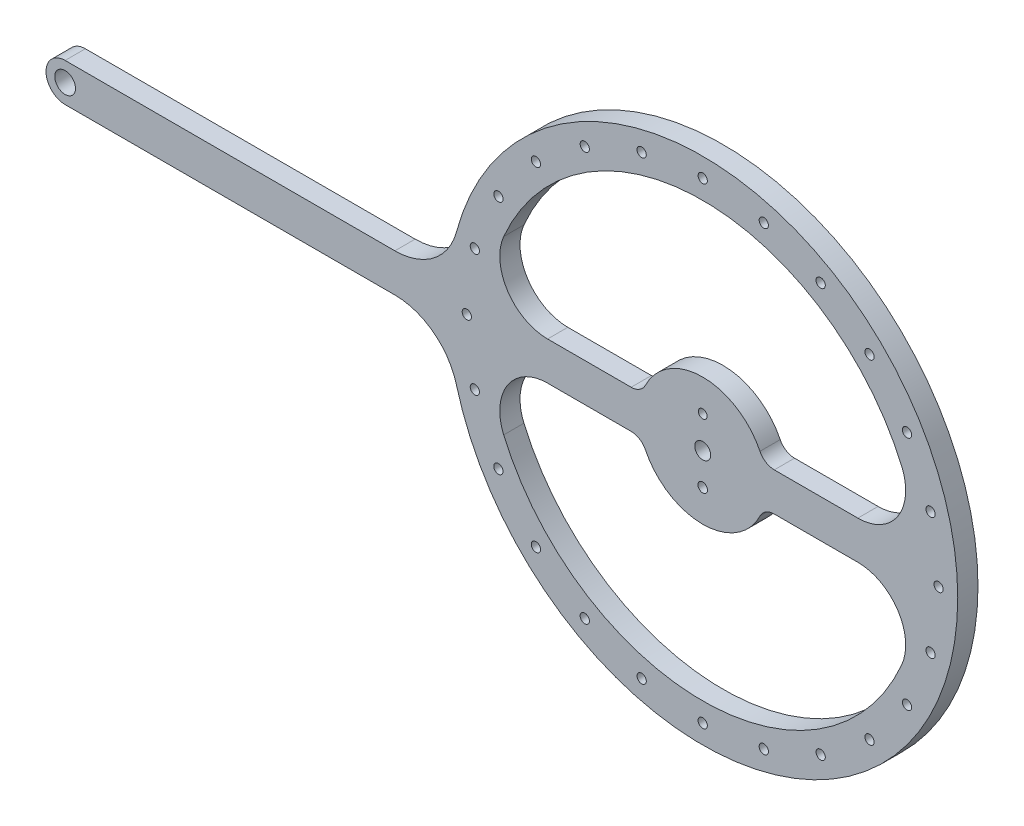
SolidWorks part; units mm, degrees
ref_plane "Front Plane" through (0, 0, 0) normal (0, 0, 1) x (1, 0, 0)
ref_plane "Top Plane" through (0, 0, 0) normal (0, 1, 0) x (1, 0, 0)
ref_plane "Right Plane" through (0, 0, 0) normal (1, 0, 0) x (0, 0, -1)
sketch "Sketch1" plane through (0, 0, 0) normal (0, 0, 1) x (1, 0, 0)
  line L0 (-155.3529, 10.2117) -> (-51.9137, 10.2117)
  line L1 (-4.015, 10.2117) -> (22.1972, 10.2117)
  line L2 (67.0971, 10.2117) -> (93.3092, 10.2117)
  line L3 (93.3092, 22.2117) -> (67.0971, 22.2117)
  line L4 (22.1972, 22.2117) -> (-4.015, 22.2117)
  line L5 (-51.9137, 22.2117) -> (-155.3529, 22.2117)
  arc A0 (-32.6016, -4.5883) -> (-51.9137, 10.2117) centre (-51.9137, -9.7883) ccw
  circle A1 centre (-19.4388, -20.7883) radius 1.45
  circle A2 centre (-26.8314, -2.9409) radius 1.45
  arc A3 (-51.9137, 22.2117) -> (-32.6016, 37.0117) centre (-51.9137, 42.2117) ccw
  arc A4 (-155.3529, 22.2117) -> (-155.3529, 10.2117) centre (-155.3529, 16.2117) ccw
  circle A5 centre (-155.3529, 16.2117) radius 3.25
  circle A6 centre (-26.8314, 35.3643) radius 1.45
  circle A7 centre (-19.4388, 53.2117) radius 1.45
  circle A8 centre (-29.3529, 16.2117) radius 1.45
  arc A9 (107.0815, -10.7317) -> (93.3092, 10.2117) centre (93.3092, -4.7883) ccw
  arc A10 (-4.015, 10.2117) -> (-17.7873, -10.7317) centre (-4.015, -4.7883) ccw
  arc A11 (67.0971, 10.2117) -> (62.6071, 7.4117) centre (67.0971, 5.2117) ccw
  arc A12 (26.6872, 7.4117) -> (22.1972, 10.2117) centre (22.1972, 5.2117) ccw
  circle A13 centre (44.6471, 6.2117) radius 1.5
  circle A14 centre (116.1256, -2.9409) radius 1.45
  circle A15 centre (108.733, -20.7883) radius 1.45
  circle A16 centre (96.973, -36.1142) radius 1.45
  circle A17 centre (81.6471, -47.8742) radius 1.45
  circle A18 centre (63.7997, -55.2668) radius 1.45
  circle A19 centre (44.6471, -57.7883) radius 1.45
  circle A20 centre (25.4945, -55.2668) radius 1.45
  circle A21 centre (7.6471, -47.8742) radius 1.45
  circle A22 centre (-7.6788, -36.1142) radius 1.45
  arc A23 (124.5879, 13.1348) -> (-32.6016, 37.0117) centre (44.6471, 16.2117) ccw
  arc A24 (-32.6016, -4.5883) -> (124.5879, 13.1348) centre (44.6471, 16.2117) ccw
  arc A25 (-17.7873, -10.7317) -> (107.0815, -10.7317) centre (44.6471, 16.2117) ccw
  arc A26 (107.0815, 43.1551) -> (-17.7873, 43.1551) centre (44.6471, 16.2117) ccw
  arc A27 (26.6872, 7.4117) -> (62.6071, 7.4117) centre (44.6471, 16.2117) ccw
  arc A28 (62.6071, 25.0117) -> (26.6872, 25.0117) centre (44.6471, 16.2117) ccw
  arc A29 (93.3092, 22.2117) -> (107.0815, 43.1551) centre (93.3092, 37.2117) ccw
  arc A30 (-17.7873, 43.1551) -> (-4.015, 22.2117) centre (-4.015, 37.2117) ccw
  arc A31 (62.6071, 25.0117) -> (67.0971, 22.2117) centre (67.0971, 27.2117) ccw
  arc A32 (22.1972, 22.2117) -> (26.6872, 25.0117) centre (22.1972, 27.2117) ccw
  circle A33 centre (44.6471, 16.2117) radius 2.5
  circle A34 centre (-7.6788, 68.5376) radius 1.45
  circle A35 centre (7.6471, 80.2976) radius 1.45
  circle A36 centre (25.4945, 87.6902) radius 1.45
  circle A37 centre (44.6471, 90.2117) radius 1.45
  circle A38 centre (63.7997, 87.6902) radius 1.45
  circle A39 centre (81.6471, 80.2976) radius 1.45
  circle A40 centre (96.973, 68.5376) radius 1.45
  circle A41 centre (108.733, 53.2117) radius 1.45
  circle A42 centre (116.1256, 35.3643) radius 1.45
  circle A43 centre (44.6471, 26.2117) radius 1.375
  circle A44 centre (118.6471, 16.2117) radius 1.45
  dimension "D1" = 5
  dimension "D2" = 80
extrude "Boss-Extrude2" add sketch "Sketch1" along normal blind 6.35
